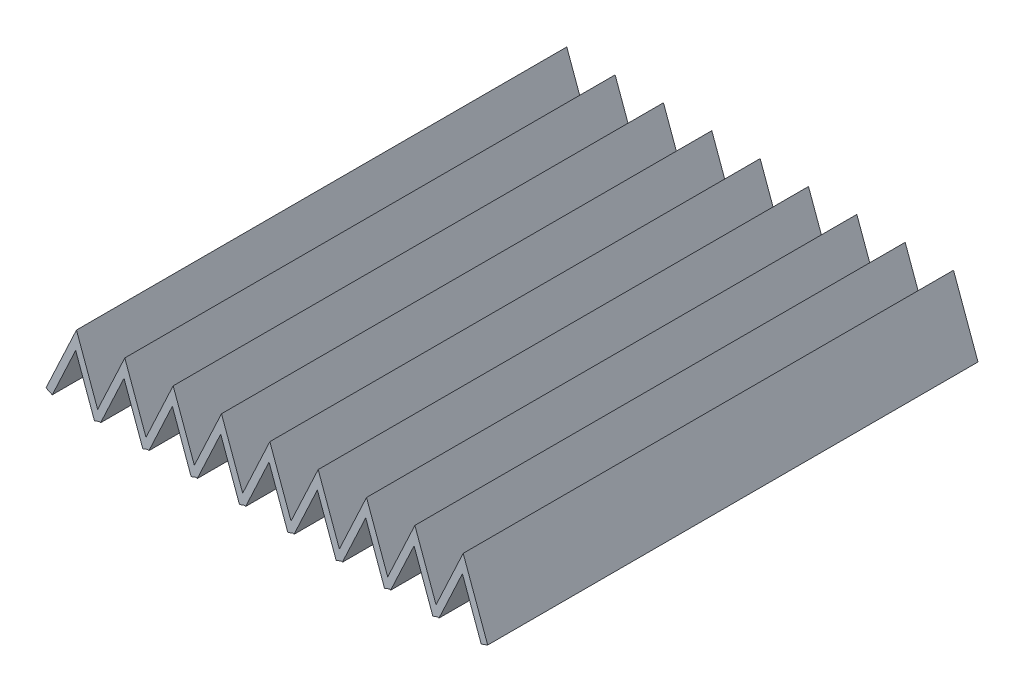
SolidWorks part; units mm, degrees
ref_plane "Front Plane" through (0, 0, 0) normal (0, 0, 1) x (1, 0, 0)
ref_plane "Top Plane" through (0, 0, 0) normal (0, 1, 0) x (1, 0, 0)
ref_plane "Right Plane" through (0, 0, 0) normal (1, 0, 0) x (0, 0, -1)
sketch "Sketch1" plane through (0, 0, 0) normal (0, 0, 1) x (1, 0, 0)
  line L0 (0, 0) -> (11.2022, 24.0231)
  line L1 (11.2022, 24.0231) -> (20.2034, -0.7074)
  line L3 (0, -55) -> (0, 55) construction
  dimension "D1" = 45
  dimension "D2" = 25
extrude "Extrude-Thin1" add sketch "Sketch1" against normal blind 180.34 thin
pattern_linear "LPattern1" count 2 spacing 20.32 count 9 spacing 17.78 along (1, 0, 0) of "Extrude-Thin1"
